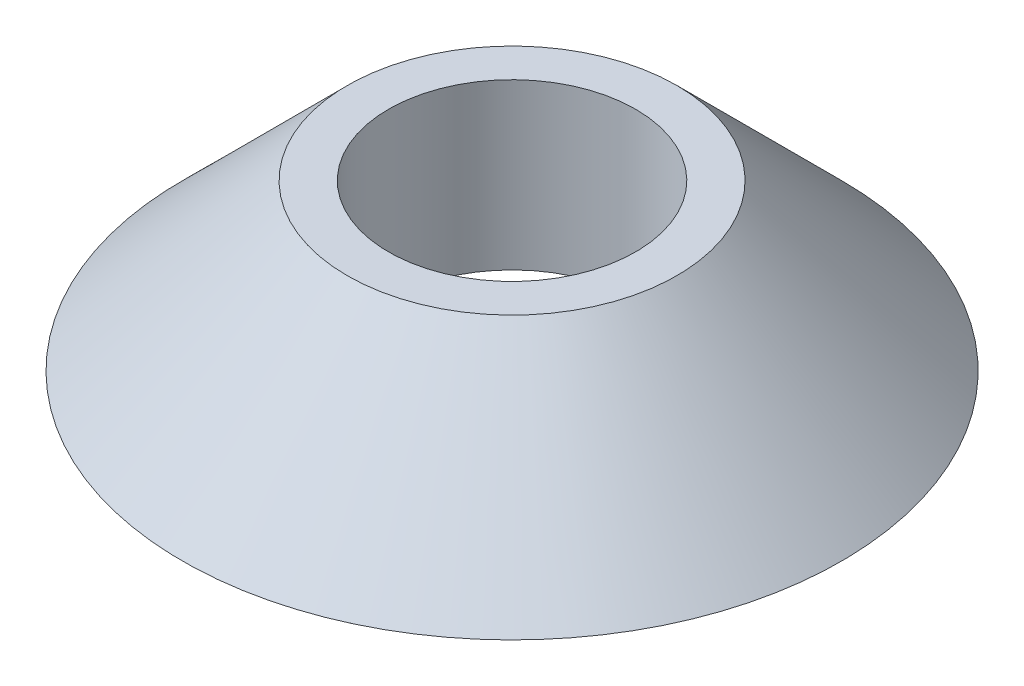
SolidWorks part; units mm, degrees
ref_plane "Front Plane" through (0, 0, 0) normal (0, 0, 1) x (1, 0, 0)
ref_plane "Top Plane" through (0, 0, 0) normal (0, 1, 0) x (1, 0, 0)
ref_plane "Right Plane" through (0, 0, 0) normal (1, 0, 0) x (0, 0, -1)
sketch "Sketch1" plane through (0, 0, 0) normal (0, 0, 1) x (1, 0, 0)
  line L0 (0, -1000.6938) -> (0, 48999.3062) construction
  line L1 (9.525, 0) -> (25.4, 0)
  line L2 (25.4, 0) -> (12.7, 12.7)
  line L3 (12.7, 12.7) -> (9.525, 12.7)
  line L4 (9.525, 12.7) -> (0, 12.7) construction
  line L5 (9.525, 12.7) -> (9.525, 0)
  line L6 (0, 0) -> (9.525, 0) construction
  dimension "D1" = 45
  dimension "D2" = 12.7
  dimension "D3" = 12.7
  dimension "D4" = 19.05
revolve "Revolve1" add sketch "Sketch1" angle 360 about L0
